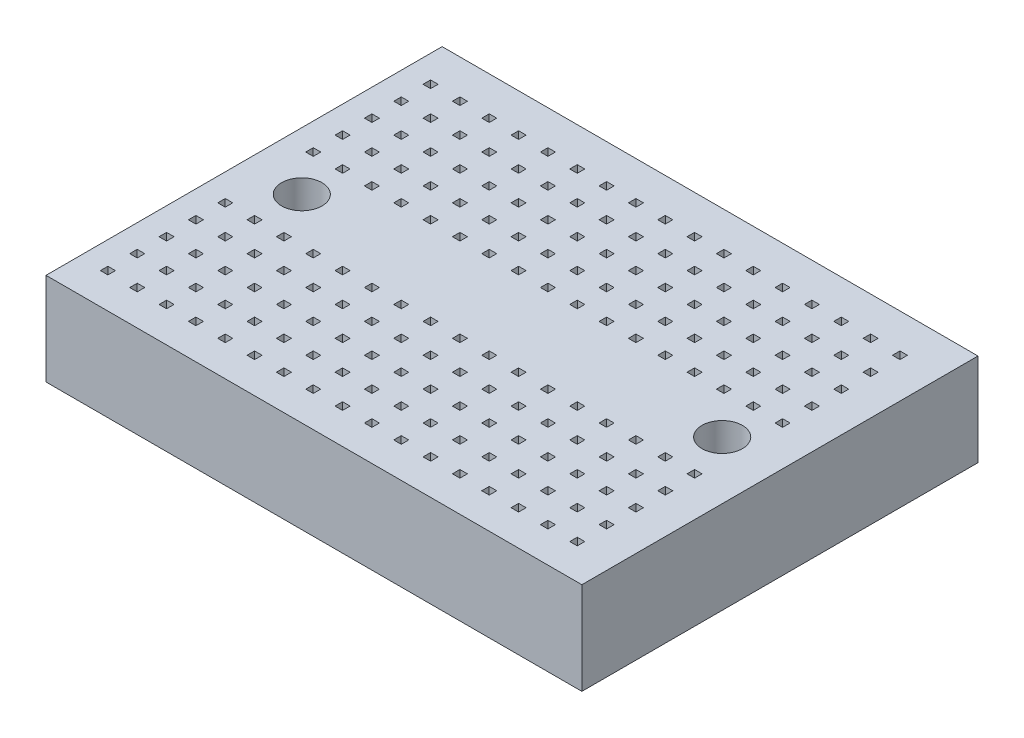
SolidWorks part; units mm, degrees
ref_plane "Front" through (0, 0, 0) normal (0, 0, 1) x (1, 0, 0)
ref_plane "Top" through (0, 0, 0) normal (0, 1, 0) x (1, 0, 0)
ref_plane "Right" through (0, 0, 0) normal (1, 0, 0) x (0, 0, -1)
sketch "草圖1" plane through (0, 0, 0) normal (0, 1, 0) x (1, 0, 0)
  line L0 (0, -17.15) -> (0, 17.15) construction
  line L1 (-23.2, -17.15) -> (23.2, -17.15)
  line L2 (-23.2, -17.15) -> (-23.2, 17.15)
  line L3 (-23.2, 17.15) -> (23.2, 17.15)
  line L4 (23.2, -17.15) -> (23.2, 17.15)
  line L5 (-23.2, -17.15) -> (23.2, 17.15) construction
  line L6 (-23.2, 17.15) -> (23.2, -17.15) construction
  point P0 (0, 0)
  dimension "D1" = 34.3
  dimension "D2" = 46.4
extrude "填料-伸長1" add sketch "草圖1" along normal blind 8
sketch "草圖2" plane through (0, 8, 0) normal (0, 1, 0) x (1, 0, 0)
  line L0 (23.2, 17.15) -> (-23.2, 17.15) construction
  line L1 (-21.2, 14.15) -> (-20.55, 14.15)
  line L2 (-21.2, 14.15) -> (-21.2, 13.5)
  line L3 (-21.2, 13.5) -> (-20.55, 13.5)
  line L4 (-20.55, 14.15) -> (-20.55, 13.5)
  line L5 (-23.2, 17.15) -> (-23.2, -17.15) construction
  dimension "D1" = 0.65
  dimension "D2" = 0.65
  dimension "D3" = 3
  dimension "D4" = 2
extrude "除料-伸長1" cut sketch "草圖2" against normal blind 5
pattern_linear "直線複製排列1" count 17 spacing 2.54 along (1, 0, 0) count 12 spacing 2.54 along (0, 0, 1) skipping (0, 5), (0, 6), (1, 5), (1, 6), (2, 5), (2, 6), (3, 5), (3, 6), (4, 5), (4, 6), (5, 5), (5, 6), (6, 5), (6, 6), (7, 5), (7, 6), (8, 5), (8, 6), (9, 5), (9, 6), (10, 5), (10, 6), (11, 5), (11, 6), (12, 5), (12, 6), (13, 5), (13, 6), (14, 5), (14, 6), (15, 5), (15, 6), (16, 5), (16, 6) of "除料-伸長1"
sketch "草圖3" plane through (0, 8, 0) normal (0, 1, 0) x (1, 0, 0)
  line L0 (-18.2, 0) -> (0, 0) construction
  line L1 (0, 0) -> (18.2, 0) construction
  circle A0 centre (-18.2, 0) radius 1.75
  circle A1 centre (18.2, 0) radius 1.75
  dimension "D1" = 3.5
  dimension "D2" = 3.5
  dimension "D3" = 18.2
  dimension "D4" = 18.2
extrude "除料-伸長2" cut sketch "草圖3" against normal blind 3
sketch "草圖4" plane through (0, 5, 0) normal (0, 1, 0) x (1, 0, 0)
  circle A0 centre (-18.2, 0) radius 1
  circle A1 centre (18.2, 0) radius 1
  dimension "D1" = 2
  dimension "D2" = 2
extrude "除料-伸長3" cut sketch "草圖4" against normal blind 10
